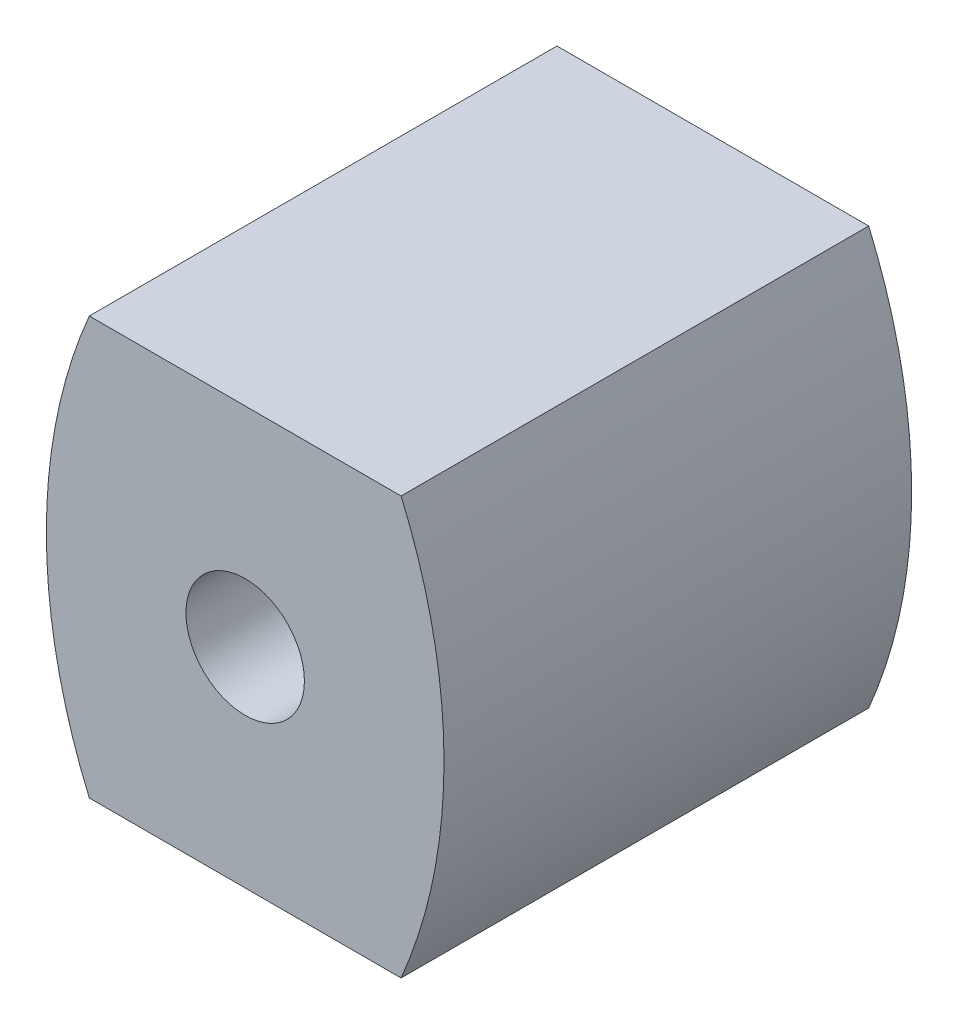
SolidWorks part; units mm, degrees
ref_plane "Alzado" through (0, 0, 0) normal (0, 0, 1) x (1, 0, 0)
ref_plane "Planta" through (0, 0, 0) normal (0, 1, 0) x (1, 0, 0)
ref_plane "Vista lateral" through (0, 0, 0) normal (1, 0, 0) x (0, 0, -1)
sketch "Croquis1" plane through (0, 0, 0) normal (0, 0, 1) x (1, 0, 0)
  line L0 (-33.785, -22.5332) -> (-33.785, -9.1432) construction
  line L1 (-38.785, -22.5332) -> (-28.785, -22.5332)
  line L2 (-38.785, -9.1432) -> (-38.785, -22.5332) construction
  line L3 (-28.785, -9.1432) -> (-38.785, -9.1432)
  line L4 (-28.785, -9.1432) -> (-28.785, -22.5332) construction
  line L5 (20.9443, -15.8382) -> (-88.5142, -15.8382) construction
  arc A0 (-38.785, -9.1432) -> (-38.785, -22.5332) centre (-23.2042, -15.8382) ccw
  arc A1 (-28.785, -9.1432) -> (-28.785, -22.5332) centre (-44.3657, -15.8382) cw
  circle A2 centre (-33.785, -15.8382) radius 1.9
  point P11 (-33.785, -15.8382)
  dimension "D1" = 13.39
  dimension "D3" = 3.8
  dimension "D2" = 10
extrude "Saliente-Extruir2" add sketch "Croquis1" along normal blind 15 contours A1 L3 A0 L1 A2
